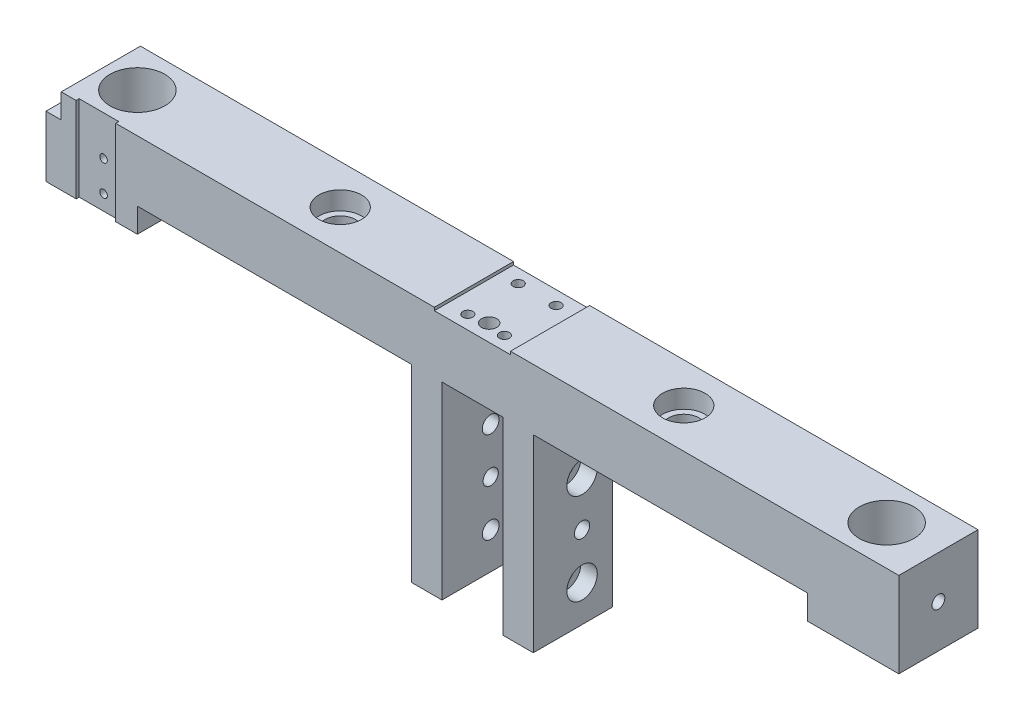
SolidWorks part; units mm, degrees
material "1.0070 (E360)"
ref_plane "前视基准面" through (0, 0, 0) normal (0, 0, 1) x (1, 0, 0)
ref_plane "上视基准面" through (0, 0, 0) normal (0, 1, 0) x (1, 0, 0)
ref_plane "右视基准面" through (0, 0, 0) normal (1, 0, 0) x (0, 0, -1)
sketch "草图1" plane through (0, 0, 0) normal (0, 0, 1) x (1, 0, 0)
  line L1 (0, 0) -> (280, 0)
  line L2 (0, 0) -> (0, 35)
  line L3 (0, 35) -> (280, 35)
  line L4 (280, 0) -> (280, 35)
  dimension "D1" = 280
  dimension "D2" = 35
extrude "凸台-拉伸1" add sketch "草图1" along normal blind 26
sketch "草图3" plane through (0, 0, 0) normal (0, -1, 0) x (1, 0, 0)
  line L0 (0, 13) -> (280, 13) construction
  line L1 (0, 26) -> (0, 0) construction
  line L2 (280, 26) -> (280, 0) construction
  line L3 (280, 13) -> (140, 13) construction
  line L4 (140, 13) -> (140, -29.0433) construction
  circle A0 centre (17, 13) radius 9
  circle A1 centre (263, 13) radius 9
  dimension "D1" = 18
  dimension "D2" = 246
extrude "切除-拉伸1" cut sketch "草图3" against normal through all
sketch "草图4" plane through (0, 35, 0) normal (0, 1, 0) x (1, 0, 0)
  line L0 (140, -26) -> (140, 0) construction
  line L1 (280, -26) -> (0, -26) construction
  line L2 (280, 0) -> (0, 0) construction
  line L4 (152.5, -26) -> (127.5, -26)
  line L5 (152.5, -26) -> (152.5, 0)
  line L6 (152.5, 0) -> (127.5, 0)
  line L7 (127.5, -26) -> (127.5, 0)
  dimension "D1" = 25
extrude "切除-拉伸2" cut sketch "草图4" against normal blind 1
hole_wizard "M4 螺纹孔1" positions "草图5" profile "草图6" tap size "M4" standard "ISO"
sketch "草图5" plane through (0, 34, 0) normal (0, 1, 0) x (1, 0, 0)
  point P0 (146, -21.5)
  point P3 (134, -21.5)
  point P6 (146, -4.5)
  point P9 (133.547, -4.5)
sketch "草图6" plane through (146, 34, 21.5) normal (1, 0, 0) x (0, 0, 1)
  line L0 (0, 0) -> (0, 11.0914)
  line L1 (0, 11.0914) -> (1.65, 10.1)
  line L2 (1.65, 10.1) -> (1.65, 0)
  line L5 (1.65, 0) -> (0, 0)
  line L10 (0, 11.0914) -> (-1.65, 10.1) construction
  line L11 (0, -6.35) -> (0, 107.95) construction
  dimension "螺纹孔钻头直径" = 3.3
  dimension "螺纹孔钻头深度" = 10.1
  dimension "导头角度" = 118
cosmetic thread "孔螺蚊线1" parameters "D1"=8, "D2"=4
cosmetic thread "孔螺蚊线2" parameters "D1"=8, "D2"=4
cosmetic thread "孔螺蚊线3" parameters "D1"=8, "D2"=4
cosmetic thread "孔螺蚊线4" parameters "D1"=8, "D2"=4
sketch "草图7" plane through (0, 0, 26) normal (0, 0, 1) x (1, 0, 0)
  line L0 (140, 0) -> (140, 47.7529) construction
  line L1 (0, 0) -> (280, 0) construction
  line L3 (250, 0) -> (30, 0)
  line L4 (250, 0) -> (250, 15)
  line L5 (250, 15) -> (30, 15)
  line L6 (30, 0) -> (30, 15)
  dimension "D1" = 220
  dimension "D2" = 15
extrude "切除-拉伸3" cut sketch "草图7" against normal through all
sketch "草图8" plane through (0, 15, 0) normal (0, -1, 0) x (1, 0, 0)
  line L0 (140, 0) -> (140, 26) construction
  line L1 (250, 0) -> (30, 0) construction
  line L2 (250, 26) -> (30, 26) construction
  line L4 (160, 0) -> (120, 0)
  line L5 (160, 0) -> (160, 26)
  line L6 (160, 26) -> (120, 26)
  line L7 (120, 0) -> (120, 26)
  dimension "D1" = 40
extrude "凸台-拉伸2" add sketch "草图8" along normal blind 35
sketch "草图15" plane through (0, -20, 0) normal (0, -1, 0) x (1, 0, 0)
  line L1 (160, 26) -> (101.5693, 26)
  line L2 (160, 26) -> (160, -18.3762)
  line L3 (160, -18.3762) -> (101.5693, -18.3762)
  line L4 (101.5693, 26) -> (101.5693, -18.3762)
extrude "切除-拉伸7" cut sketch "草图15" against normal blind 3
sketch "草图17" plane through (0, -17, 0) normal (0, -1, 0) x (1, 0, 0)
  line L1 (120, 0) -> (160, 0)
  line L2 (120, 0) -> (120, 26)
  line L3 (120, 26) -> (160, 26)
  line L4 (160, 0) -> (160, 26)
extrude "凸台-拉伸4" add sketch "草图17" along normal blind 30
sketch "草图18" plane through (0, 0, 0) normal (0, 0, -1) x (-1, 0, 0)
  line L0 (-140, -47) -> (-140, 34) construction
  line L1 (-120, -47) -> (-160, -47) construction
  line L2 (-152.5, 34) -> (-127.5, 34) construction
  line L4 (-130, -47) -> (-150, -47)
  line L5 (-130, -47) -> (-130, 15)
  line L6 (-130, 15) -> (-150, 15)
  line L7 (-150, -47) -> (-150, 15)
  dimension "D1" = 20
  dimension "D2" = 19
extrude "切除-拉伸8" cut sketch "草图18" against normal through all
sketch "草图19" plane through (0, 0, 0) normal (0, -1, 0) x (1, 0, 0)
  line L1 (280, 0) -> (250, 0)
  line L2 (280, 0) -> (280, 26)
  line L3 (280, 26) -> (250, 26)
  line L4 (250, 0) -> (250, 26)
  line L5 (30, 26) -> (0, 26)
  line L6 (30, 26) -> (30, 0)
  line L7 (30, 0) -> (0, 0)
  line L8 (0, 26) -> (0, 0)
extrude "切除-拉伸11" cut sketch "草图19" against normal blind 7
hole_wizard "M5 螺纹孔1" positions "草图20" profile "草图21" tap size "M5" standard "ISO"
sketch "草图20" plane through (280, 0, 0) normal (1, 0, 0) x (0, 0, -1)
  line L0 (-13, 7) -> (-13, 35) construction
  line L1 (0, 7) -> (-26, 7) construction
  line L2 (-26, 35) -> (0, 35) construction
  line L3 (-13, 35) -> (-13, 21) construction
  point P0 (-13, 21)
sketch "草图21" plane through (280, 21, 13) normal (0, 1, 0) x (0, 0, -1)
  line L0 (0, 0) -> (0, 13.6618)
  line L1 (0, 13.6618) -> (2.1, 12.4)
  line L2 (2.1, 12.4) -> (2.1, 0)
  line L5 (2.1, 0) -> (0, 0)
  line L10 (0, 13.6618) -> (-2.1, 12.4) construction
  line L11 (0, -6.35) -> (0, 107.95) construction
  dimension "螺纹孔钻头直径" = 4.2
  dimension "螺纹孔钻头深度" = 12.4
  dimension "导头角度" = 118
cosmetic thread "孔螺蚊线5" parameters "D1"=8.2484, "D2"=5
ref_plane "基准面1" through (140, 0, 0) normal (-1, 0, 0) x (0, 0, 1)
mirror "镜向1" about plane through (140, 0, 0) normal (-1, 0, 0) of "M5 螺纹孔1"
hole_wizard "M5 六角凹头螺钉的柱形沉头孔1" positions "草图23" profile "草图24" counterbore size "M5" standard "ISO"
sketch "草图23" plane through (160, 0, 0) normal (1, 0, 0) x (0, 0, -1)
  line L0 (0, -47) -> (0, 15) construction
  line L1 (0, 15) -> (-26, 15) construction
  point P0 (-10, -35)
  point P2 (-10, -5)
  dimension "D1" = 10
  dimension "D2" = 20
  dimension "D3" = 30
sketch "草图24" plane through (160, -35, 10) normal (0, 1, 0) x (0, 0, -1)
  line L0 (0, 0) -> (0, 14.0524)
  line L1 (0, 14.0524) -> (2.75, 12.4)
  line L2 (2.75, 12.4) -> (2.75, 5.4)
  line L3 (2.75, 5.4) -> (5, 5.4)
  line L4 (5, 5.4) -> (5, 0)
  line L5 (5, 0) -> (0, 0)
  line L10 (0, 14.0524) -> (-2.75, 12.4) construction
  line L11 (0, -6.35) -> (0, 107.95) construction
  dimension "孔直径" = 5.5
  dimension "孔深度" = 12.4
  dimension "柱形沉头孔直径" = 10
  dimension "柱形沉头孔深度" = 5.4
  dimension "导头角度" = 118
chamfer "倒角1" distance 5 angle 30 1 edges at (150, -16, 0)
chamfer "倒角2" distance 5 angle 30 1 edges at (130, -16, 0)
mirror "镜向2" about plane through (140, 0, 0) normal (-1, 0, 0) of "M5 六角凹头螺钉的柱形沉头孔1"
sketch "草图25" plane through (0, 15, 0) normal (0, -1, 0) x (1, 0, 0)
  line L0 (140, 26) -> (140, 15.3347) construction
  line L1 (130, 26) -> (150, 26) construction
  circle A0 centre (140, 20.4973) radius 2.5
  dimension "D1" = 5
  dimension "D2" = 5.5027
extrude "切除-拉伸12" cut sketch "草图25" against normal through all
sketch "草图26" plane through (120, 0, 0) normal (-1, 0, 0) x (0, 0, 1)
  line L0 (10, -30) -> (10, -10) construction
  line L1 (10, -10) -> (10, -20) construction
  line L2 (10, -20) -> (27.1215, -20) construction
  circle A0 centre (10, -35) radius 5 construction
  circle A1 centre (10, -5) radius 5 construction
  circle A2 centre (10, -20) radius 2.5
  dimension "D1" = 5
extrude "切除-拉伸13" cut sketch "草图26" against normal through all
sketch "草图27" plane through (0, 35, 0) normal (0, 1, 0) x (1, 0, 0)
  line L0 (152.5, -13) -> (127.5, -13) construction
  line L1 (152.5, -26) -> (152.5, 0) construction
  line L2 (127.5, 0) -> (127.5, -26) construction
  line L3 (127.5, -13) -> (140, -13) construction
  line L4 (140, -13) -> (140, -58.2295) construction
  circle A0 centre (196.4, -13) radius 5
  circle A1 centre (83.6, -13) radius 5
  dimension "D1" = 10
extrude "切除-拉伸14" cut sketch "草图27" against normal through all
sketch "草图28" plane through (0, 35, 0) normal (0, 1, 0) x (1, 0, 0)
  circle A0 centre (196.4, -13) radius 7
  circle A1 centre (83.6, -13) radius 7
  dimension "D1" = 14
  dimension "D2" = 14
extrude "切除-拉伸15" cut sketch "草图28" against normal blind 6
sketch "草图31" plane through (0, 0, 26) normal (0, 0, 1) x (1, 0, 0)
  line L0 (30, 7) -> (0, 7) construction
  line L1 (22.9, 7) -> (9.9, 7)
  line L2 (22.9, 7) -> (22.9, 35)
  line L3 (22.9, 35) -> (9.9, 35)
  line L4 (9.9, 7) -> (9.9, 35)
  line L5 (127.5, 35) -> (0, 35) construction
  line L6 (0, 35) -> (0, 7) construction
  dimension "D1" = 13
  dimension "D2" = 9.9
extrude "切除-拉伸16" cut sketch "草图31" against normal blind 1
hole_wizard "M3 螺纹孔1" positions "草图32" profile "草图33" tap size "M3" standard "ISO"
sketch "草图32" plane through (0, 0, 25) normal (0, 0, 1) x (1, 0, 0)
  point P0 (17.9, 12)
  point P3 (17.9, 22)
sketch "草图33" plane through (17.9, 12, 25) normal (1, 0, 0) x (0, -1, 0)
  line L0 (0, 0) -> (0, 8.2511)
  line L1 (0, 8.2511) -> (1.25, 7.5)
  line L2 (1.25, 7.5) -> (1.25, 0)
  line L5 (1.25, 0) -> (0, 0)
  line L10 (0, 8.2511) -> (-1.25, 7.5) construction
  line L11 (0, -6.35) -> (0, 107.95) construction
  dimension "螺纹孔钻头直径" = 2.5
  dimension "螺纹孔钻头深度" = 7.5
  dimension "导头角度" = 118
cosmetic thread "孔螺蚊线6" parameters "D1"=3.2606, "D2"=3
cosmetic thread "孔螺蚊线7" parameters "D1"=3.2606, "D2"=3
sketch "草图34" plane through (0, 0, 26) normal (0, 0, 1) x (1, 0, 0)
  line L0 (140, 15) -> (140, 34) construction
  line L1 (0, 35) -> (5, 35)
  line L2 (0, 35) -> (0, 27)
  line L3 (0, 27) -> (5, 27)
  line L4 (5, 35) -> (5, 27)
  line L5 (130, 15) -> (150, 15) construction
  line L6 (127.5, 34) -> (152.5, 34) construction
  dimension "D1" = 8
  dimension "D2" = 5
extrude "切除-拉伸17" cut sketch "草图34" against normal through all
